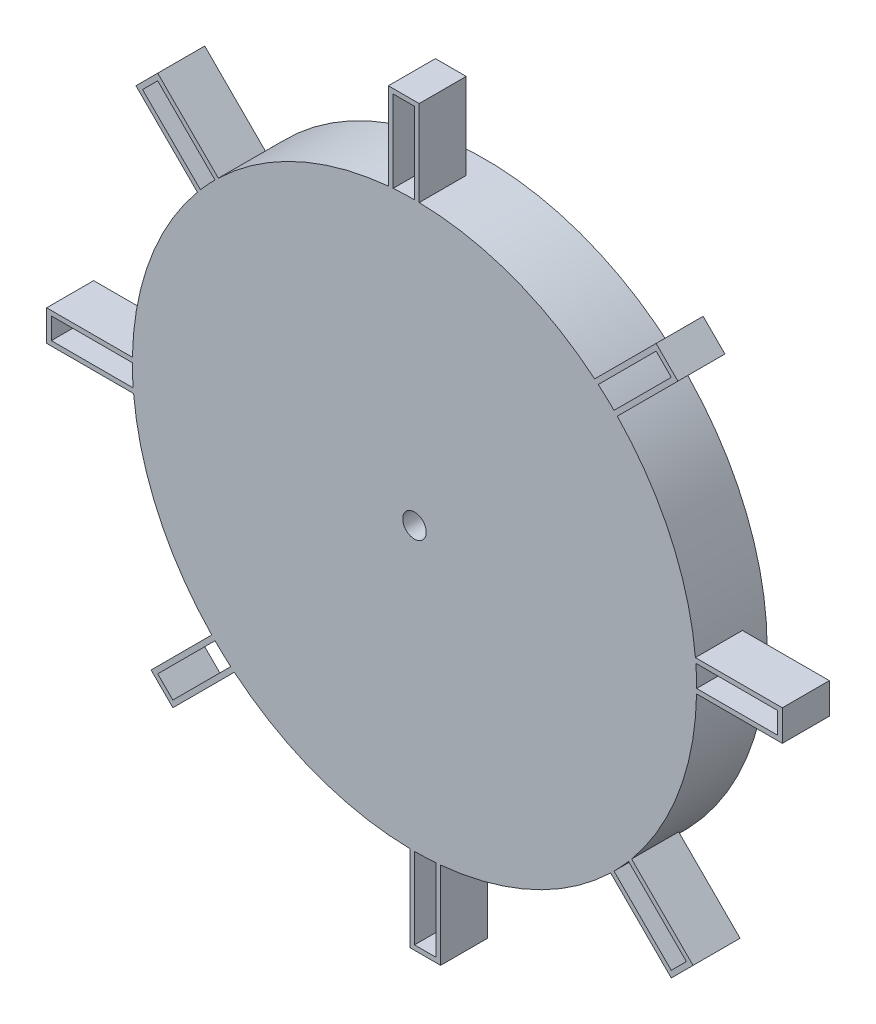
SolidWorks part; units mm, degrees
ref_plane "Front Plane" through (0, 0, 0) normal (0, 0, 1) x (1, 0, 0)
ref_plane "Top Plane" through (0, 0, 0) normal (0, 1, 0) x (1, 0, 0)
ref_plane "Right Plane" through (0, 0, 0) normal (1, 0, 0) x (0, 0, -1)
sketch "Sketch1" plane through (0, 0, 0) normal (0, 0, 1) x (1, 0, 0)
  circle A0 centre (0, 0) radius 60
  circle A1 centre (0, 0) radius 2.5
extrude "Boss-Extrude1" add sketch "Sketch1" along normal blind 15
sketch "Sketch3" plane through (0, 0, 15) normal (0, 0, 1) x (1, 0, 0)
  line L0 (-4.5552, 59.8268) -> (-4.5552, 77.229)
  line L1 (-4.5552, 77.229) -> (0, 77.229)
  line L2 (0, 77.229) -> (0, 60)
  line L3 (39.083, 45.5249) -> (51.3882, 57.8302)
  line L4 (51.3882, 57.8302) -> (54.6092, 54.6092)
  line L5 (54.6092, 54.6092) -> (42.4264, 42.4264)
  line L6 (59.8268, 4.5552) -> (77.229, 4.5552)
  line L7 (77.229, 4.5552) -> (77.229, 0)
  line L8 (77.229, 0) -> (60, 0)
  line L9 (45.5249, -39.083) -> (57.8302, -51.3882)
  line L10 (57.8302, -51.3882) -> (54.6092, -54.6092)
  line L11 (54.6092, -54.6092) -> (42.4264, -42.4264)
  line L12 (4.5552, -59.8268) -> (4.5552, -77.229)
  line L13 (4.5552, -77.229) -> (0, -77.229)
  line L14 (0, -77.229) -> (0, -60)
  line L15 (-39.083, -45.5249) -> (-51.3882, -57.8302)
  line L16 (-51.3882, -57.8302) -> (-54.6092, -54.6092)
  line L17 (-54.6092, -54.6092) -> (-42.4264, -42.4264)
  line L18 (-59.8268, -4.5552) -> (-77.229, -4.5552)
  line L19 (-77.229, -4.5552) -> (-77.229, 0)
  line L20 (-77.229, 0) -> (-60, 0)
  line L21 (-45.5249, 39.083) -> (-57.8302, 51.3882)
  line L22 (-57.8302, 51.3882) -> (-54.6092, 54.6092)
  line L23 (-54.6092, 54.6092) -> (-42.4264, 42.4264)
  circle A0 centre (0, 0) radius 60 construction
  arc A1 (-4.5552, 59.8268) -> (0, 60) centre (0, 0) cw
  arc A2 (-45.5249, 39.083) -> (-42.4264, 42.4264) centre (0, 0) cw
  arc A3 (-59.8268, -4.5552) -> (-60, 0) centre (0, 0) cw
  arc A4 (-39.083, -45.5249) -> (-42.4264, -42.4264) centre (0, 0) cw
  arc A5 (0, -60) -> (4.5552, -59.8268) centre (0, 0) ccw
  arc A6 (42.4264, -42.4264) -> (45.5249, -39.083) centre (0, 0) ccw
  arc A7 (60, 0) -> (59.8268, 4.5552) centre (0, 0) ccw
  arc A8 (42.4264, 42.4264) -> (39.083, 45.5249) centre (0, 0) ccw
  point P39 (0, 0)
  dimension "D1" = 8
extrude "Extrude-Thin2" add sketch "Sketch3" against normal blind 10 thin thin type one direction wall 1
